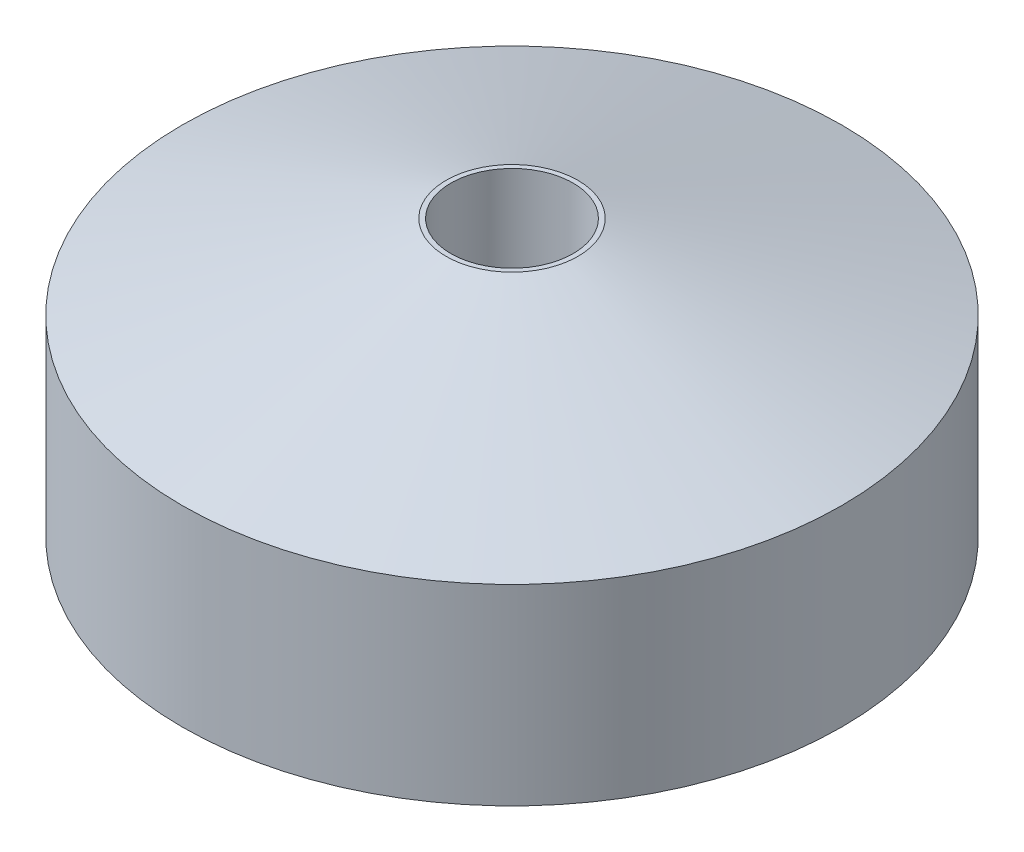
SolidWorks part; units mm, degrees
material "7075-T6 (SN)"
ref_plane "Front Plane" through (0, 0, 0) normal (0, 0, 1) x (1, 0, 0)
ref_plane "Top Plane" through (0, 0, 0) normal (0, 1, 0) x (1, 0, 0)
ref_plane "Right Plane" through (0, 0, 0) normal (1, 0, 0) x (0, 0, -1)
sketch "Sketch1" plane through (0, 0, 0) normal (0, 1, 0) x (1, 0, 0)
  circle A0 centre (0, 0) radius 27.5
  dimension "D1" = 55
extrude "Boss-Extrude1" add sketch "Sketch1" along normal blind 23
sketch "Sketch3" plane through (0, 0, 0) normal (1, 0, 0) x (0, 0, -1)
  line L0 (27.5, 23) -> (-27.5, 23) construction
  line L3 (-27.5, 23) -> (-27.5, 0) construction
  line L4 (-27.5, 0) -> (27.5, 0) construction
  line L5 (-27.5, 16) -> (-5.5, 23)
  line L6 (-5.5, 23) -> (-27.5, 23)
  line L7 (-27.5, 23) -> (-27.5, 16)
  point P0 (-5.5, 23)
  point P1 (-27.5, 16)
  dimension "D1" = 22
  dimension "D2" = 16
sketch3d "3DSketch1"
  line L0 (0, 0, 0) -> (0, 27.8957, 0)
revolve "Cut-Revolve1" cut sketch "Sketch3" angle 360 about L0
sketch "Sketch4" plane through (0, 23, 0) normal (0, 1, 0) x (1, 0, 0)
  point P0 (0, 0)
hole_wizard "M12x1.75 Tapped Hole1" positions "3DSketch2" profile "Sketch6" tap size "M12x1.75" standard "ANSI Metric"
sketch3d "3DSketch2"
  point P0 (0, 23, 0)
sketch "Sketch6" plane through (0, 23, 0) normal (1, 0, 0) x (0, 0, 1)
  line L0 (0, 0) -> (0, 24.0644)
  line L1 (0, 24.0644) -> (5.1, 21)
  line L2 (5.1, 21) -> (5.1, 0)
  line L5 (5.1, 0) -> (0, 0)
  line L10 (0, 24.0644) -> (-5.1, 21) construction
  line L11 (0, -6.35) -> (0, 107.95) construction
  dimension "Tap Drill Dia." = 10.2
  dimension "Tap Drill Depth" = 21
  dimension "Drill Angle" = 118
cosmetic thread "Hole Thread1" parameters "D1"=20, "D2"=12
sketch "Sketch7" plane through (0, 0, 0) normal (0, -1, 0) x (1, 0, 0)
  circle A0 centre (0, 0) radius 31 construction
  point P3 (0, 31)
  point P4 (26.8468, 15.5)
  point P10 (26.8468, -15.5)
  point P11 (0, -31)
  point P12 (-26.8468, -15.5)
  point P13 (-26.8468, 15.5)
  dimension "D1" = 62
  dimension "D2" = 6
sketch "Sketch9" plane through (0, 0, 0) normal (0, -1, 0) x (1, 0, 0)
  circle A0 centre (0, 0) radius 11
  dimension "D1" = 22
extrude "Cut-Extrude1" cut sketch "Sketch9" against normal blind 10
sketch "Sketch11" plane through (0, 0, 0) normal (0, -1, 0) x (1, 0, 0)
  circle A0 centre (0, 0) radius 20
  point P3 (0, 20)
  point P7 (20, 0)
  point P8 (0, -20)
  point P9 (-20, 0)
  dimension "D1" = 40
  dimension "D2" = 4
hole_wizard "M8x1.25 Tapped Hole1" positions "3DSketch4" profile "Sketch12" tap size "M8x1.25" standard "ANSI Metric"
sketch3d "3DSketch4"
  point P0 (0, 0, 20)
  point P3 (20, 0, 0)
  point P6 (0, 0, -20)
  point P9 (-20, 0, 0)
sketch "Sketch12" plane through (0, 0, 20) normal (1, 0, 0) x (0, 0, -1)
  line L0 (0, 0) -> (0, 18.0429)
  line L1 (0, 18.0429) -> (3.4, 16)
  line L2 (3.4, 16) -> (3.4, 0)
  line L5 (3.4, 0) -> (0, 0)
  line L10 (0, 18.0429) -> (-3.4, 16) construction
  line L11 (0, -6.35) -> (0, 107.95) construction
  dimension "Tap Drill Dia." = 6.8
  dimension "Tap Drill Depth" = 16
  dimension "Drill Angle" = 118
cosmetic thread "Hole Thread2" parameters "D1"=14, "D2"=8
cosmetic thread "Hole Thread3" parameters "D1"=14, "D2"=8
cosmetic thread "Hole Thread4" parameters "D1"=14, "D2"=8
cosmetic thread "Hole Thread5" parameters "D1"=14, "D2"=8
